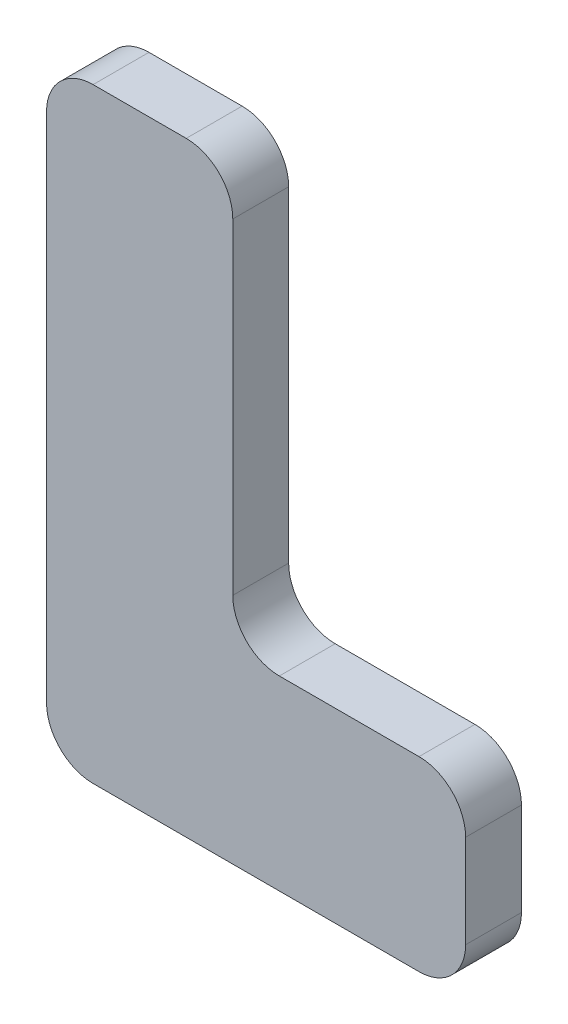
SolidWorks part; units mm, degrees
ref_plane "Front Plane" through (0, 0, 0) normal (0, 0, 1) x (1, 0, 0)
ref_plane "Top Plane" through (0, 0, 0) normal (0, 1, 0) x (1, 0, 0)
ref_plane "Right Plane" through (0, 0, 0) normal (1, 0, 0) x (0, 0, -1)
sketch "Sketch1" plane through (0, 0, 0) normal (0, 0, 1) x (1, 0, 0)
  line L0 (-107.5309, 110.3022) -> (-107.5309, 0.3022)
  line L1 (-97.5309, 120.3022) -> (-77.5309, 120.3022)
  line L4 (-67.5309, 110.3022) -> (-67.5309, 40.3022)
  line L5 (-97.5309, -9.6978) -> (-27.5309, -9.6978)
  line L7 (-57.5309, 30.3022) -> (-27.5309, 30.3022)
  line L8 (-17.5309, 0.3022) -> (-17.5309, 20.3022)
  arc A0 (-27.5309, -9.6978) -> (-17.5309, 0.3022) centre (-27.5309, 0.3022) ccw
  arc A1 (-27.5309, 30.3022) -> (-17.5309, 20.3022) centre (-27.5309, 20.3022) cw
  arc A2 (-77.5309, 120.3022) -> (-67.5309, 110.3022) centre (-77.5309, 110.3022) cw
  arc A3 (-97.5309, 120.3022) -> (-107.5309, 110.3022) centre (-97.5309, 110.3022) ccw
  arc A4 (-107.5309, 0.3022) -> (-97.5309, -9.6978) centre (-97.5309, 0.3022) ccw
  arc A5 (-57.5309, 30.3022) -> (-67.5309, 40.3022) centre (-57.5309, 40.3022) cw
  point P8 (-17.5309, -9.6978)
  point P11 (-17.5309, 30.3022)
  point P14 (-67.5309, 120.3022)
  point P17 (-107.5309, 120.3022)
  point P20 (-107.5309, -9.6978)
  dimension "D5" = 10
  dimension "D6" = 10
  dimension "D1" = 40
  dimension "D2" = 130
  dimension "D3" = 40
  dimension "D4" = 90
extrude "Boss-Extrude1" add sketch "Sketch1" along normal blind 12
sketch "Sketch2" plane through (0, 0, 12) normal (0, 0, 1) x (1, 0, 0)
  line L6 (-17.5309, 0.3022) -> (-17.5309, 20.3022)
  line L7 (-27.5309, 30.3022) -> (-57.5309, 30.3022)
  line L8 (-67.5309, 40.3022) -> (-67.5309, 110.3022)
  line L9 (-77.5309, 120.3022) -> (-97.5309, 120.3022)
  line L10 (-107.5309, 110.3022) -> (-107.5309, 0.3022)
  line L11 (-97.5309, -9.6978) -> (-27.5309, -9.6978)
  line L12 (-17.5309, 0.3022) -> (-17.5309, 20.3022)
  line L13 (-27.5309, 30.3022) -> (-57.5309, 30.3022)
  line L14 (-67.5309, 40.3022) -> (-67.5309, 110.3022)
  line L15 (-77.5309, 120.3022) -> (-97.5309, 120.3022)
  line L16 (-107.5309, 110.3022) -> (-107.5309, 0.3022)
  line L17 (-97.5309, -9.6978) -> (-27.5309, -9.6978)
  arc A6 (-27.5309, -9.6978) -> (-17.5309, 0.3022) centre (-27.5309, 0.3022) ccw
  arc A7 (-17.5309, 20.3022) -> (-27.5309, 30.3022) centre (-27.5309, 20.3022) ccw
  arc A8 (-67.5309, 40.3022) -> (-57.5309, 30.3022) centre (-57.5309, 40.3022) ccw
  arc A9 (-67.5309, 110.3022) -> (-77.5309, 120.3022) centre (-77.5309, 110.3022) ccw
  arc A10 (-97.5309, 120.3022) -> (-107.5309, 110.3022) centre (-97.5309, 110.3022) ccw
  arc A11 (-107.5309, 0.3022) -> (-97.5309, -9.6978) centre (-97.5309, 0.3022) ccw
  arc A12 (-27.5309, -9.6978) -> (-17.5309, 0.3022) centre (-27.5309, 0.3022) ccw
  arc A13 (-17.5309, 20.3022) -> (-27.5309, 30.3022) centre (-27.5309, 20.3022) ccw
  arc A14 (-67.5309, 40.3022) -> (-57.5309, 30.3022) centre (-57.5309, 40.3022) ccw
  arc A15 (-67.5309, 110.3022) -> (-77.5309, 120.3022) centre (-77.5309, 110.3022) ccw
  arc A16 (-97.5309, 120.3022) -> (-107.5309, 110.3022) centre (-97.5309, 110.3022) ccw
  arc A17 (-107.5309, 0.3022) -> (-97.5309, -9.6978) centre (-97.5309, 0.3022) ccw
  dimension "D1" = 0
